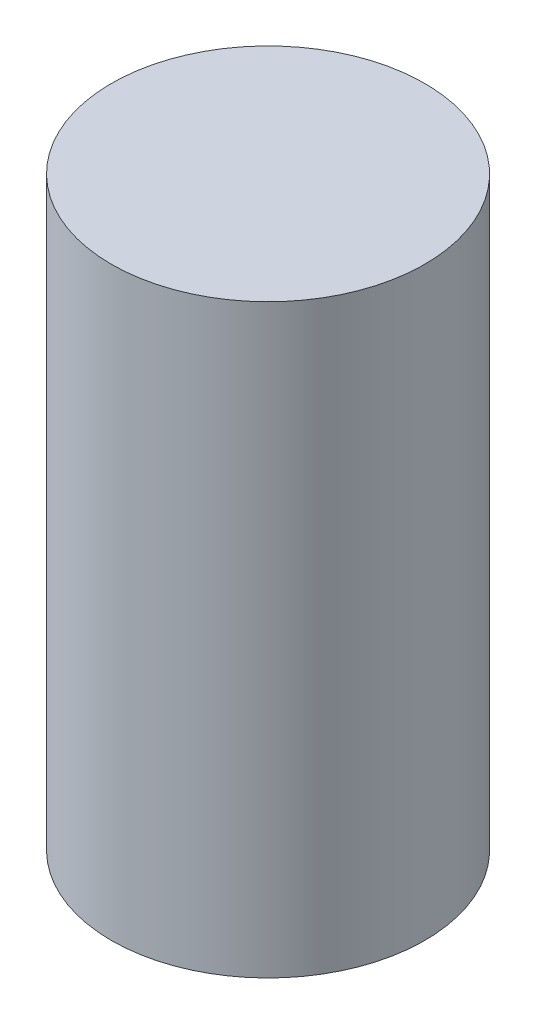
SolidWorks part; units mm, degrees
ref_plane "Front Plane" through (0, 0, 0) normal (0, 0, 1) x (1, 0, 0)
ref_plane "Top Plane" through (0, 0, 0) normal (0, 1, 0) x (1, 0, 0)
ref_plane "Right Plane" through (0, 0, 0) normal (1, 0, 0) x (0, 0, -1)
sketch "Sketch1" plane through (0, 0, 0) normal (0, 1, 0) x (1, 0, 0)
  circle A0 centre (0, 0) radius 2.675
  dimension "D1" = 5.35
extrude "Boss-Extrude1" add sketch "Sketch1" along normal blind 10
